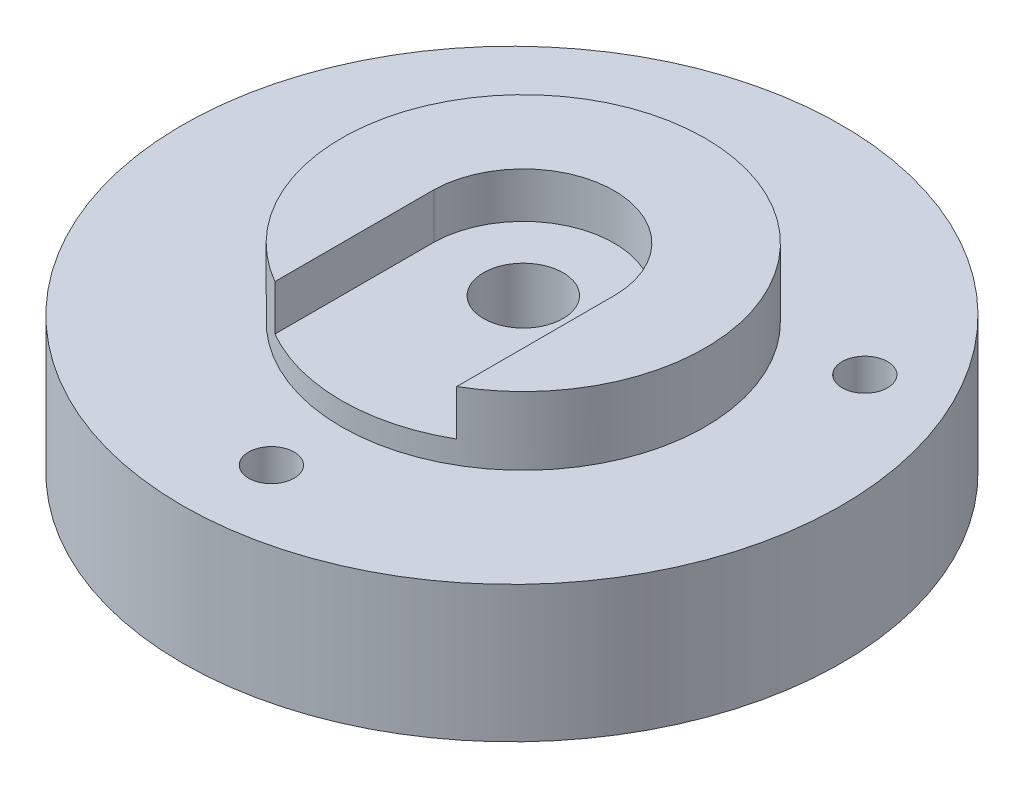
SolidWorks part; units mm, degrees
ref_plane "Front Plane" through (0, 0, 0) normal (0, 0, 1) x (1, 0, 0)
ref_plane "Top Plane" through (0, 0, 0) normal (0, 1, 0) x (1, 0, 0)
ref_plane "Right Plane" through (0, 0, 0) normal (1, 0, 0) x (0, 0, -1)
sketch "Sketch1" plane through (0, 0, 0) normal (0, 0, 1) x (1, 0, 0)
  line L1 (0, 0) -> (150, 0)
  line L2 (0, 0) -> (0, 30)
  line L3 (0, 30) -> (150, 30)
  line L4 (150, 0) -> (150, 30)
  line L5 (35, 30) -> (115, 30)
  line L6 (35, 30) -> (35, 45)
  line L7 (35, 45) -> (115, 45)
  line L8 (115, 30) -> (115, 45)
  dimension "D1" = 30
  dimension "D2" = 15
  dimension "D3" = 35
  dimension "D4" = 80
  dimension "D5" = 150
extrude "Boss-Extrude1" add sketch "Sketch1" along normal blind 145 contours L1 L4 L3 L2 | L3 L8 L7 L6
sketch "Sketch2" plane through (0, 0, 0) normal (0, 1, 0) x (1, 0, 0)
  line L1 (0, 0) -> (150, 0)
  line L2 (0, 0) -> (0, -145)
  line L3 (0, -145) -> (150, -145)
  line L4 (150, 0) -> (150, -145)
  circle A0 centre (72.5, -72.5) radius 72.5
  dimension "D1" = 145
  dimension "D2" = 72.5
  dimension "D3" = 72.5
extrude "Cut-Extrude1" cut sketch "Sketch2" along normal blind 145 contours A0 L1 L2 | A0 L2 L3 | A0 L3 L4 L1
sketch "Sketch3" plane through (0, 45, 0) normal (0, 1, 0) x (1, 0, 0)
  line L1 (35, -10.4516) -> (35, -134.5484)
  line L2 (115, -13.7633) -> (115, -131.2367)
  circle A0 centre (75, -72.5016) radius 40
  arc A1 (35, -10.4516) -> (115, -13.7633) centre (72.5, -72.5) cw
  arc A2 (35, -134.5484) -> (115, -131.2367) centre (72.5, -72.5) ccw
  arc A3 (115, -131.2367) -> (115, -13.7633) centre (72.5, -72.5) ccw construction
  arc A4 (35, -134.5484) -> (115, -131.2367) centre (72.5, -72.5) ccw construction
  arc A5 (115, -13.7633) -> (35, -10.4516) centre (72.5, -72.5) ccw construction
  line M1 (115, -131.2367) -> (115, -13.7633)
  arc M2 (115, -13.7633) -> (35, -10.4516) centre (72.5, -72.5) ccw
  line M3 (35, -10.4516) -> (35, -134.5484)
  arc M4 (35, -134.5484) -> (115, -131.2367) centre (72.5, -72.5) ccw
  dimension "D1" = 80
  dimension "D2" = 40
  dimension "D3" = 40
  dimension "D4" = 62.05
  dimension "D5" = 62.0467
extrude "Cut-Extrude2" cut sketch "Sketch3" against normal blind 15 contours A0 L2 M2 M3 | A0 L1 M4 M1
sketch "Sketch4" plane through (0, 45, 0) normal (0, 1, 0) x (1, 0, 0)
  line L0 (55, -107.1426) -> (55, -72.1426)
  line L1 (95, -107.1426) -> (95, -72.1426)
  circle A0 centre (75, -72.5016) radius 40 construction
  arc A1 (95, -107.1426) -> (55, -107.1426) centre (75, -72.5016) cw
  arc A4 (95, -72.1426) -> (55, -72.1426) centre (75, -72.5016) ccw
  circle M1 centre (75, -72.5016) radius 40
  dimension "D1" = 35
  dimension "D2" = 20
  dimension "D3" = 35
  dimension "D4" = 20
  dimension "D5" = 0
extrude "Cut-Extrude3" cut sketch "Sketch4" against normal blind 10 contours L1 A4 L0 M1
sketch "Sketch5" plane through (0, 35, 0) normal (0, 1, 0) x (1, 0, 0)
  point P0 (75, -72.5016)
hole_wizard "M20 Tapped Hole1" positions "3DSketch1" profile "Sketch6" tap size "M20" standard "ISO"
sketch3d "3DSketch1"
  point P0 (75, 35, 72.5016)
sketch "Sketch6" plane through (75, 35, 72.5016) normal (1, 0, 0) x (0, 0, 1)
  line L0 (0, 0) -> (0, 45.2575)
  line L1 (0, 45.2575) -> (8.75, 40)
  line L2 (8.75, 40) -> (8.75, 0)
  line L5 (8.75, 0) -> (0, 0)
  line L10 (0, 45.2575) -> (-8.75, 40) construction
  line L11 (0, -6.35) -> (0, 107.95) construction
  dimension "Tap Drill Dia." = 17.5
  dimension "Tap Drill Depth" = 40
  dimension "Drill Angle" = 118
cosmetic thread "Hole Thread1" parameters "D1"=20, "D2"=20
sketch "Sketch7" plane through (0, 0, 0) normal (0, 1, 0) x (1, 0, 0)
  line L0 (74.5832, 4.1452) -> (74.5832, -159.0835) construction
  line L1 (0, -72.5) -> (161.2663, -72.5) construction
  line L2 (75, -72.5016) -> (150.2505, -29.0558) construction
  line L3 (75, -72.5016) -> (-21.1007, -17.0179) construction
  circle A0 centre (72.5, -72.5) radius 72.5 construction
  circle A1 centre (74.5832, -127.5016) radius 5
  circle A2 centre (27.3686, -45.0016) radius 5
  circle A3 centre (122.6314, -45.0016) radius 5
  dimension "D2" = 10
  dimension "D7" = 10
  dimension "D8" = 10
  dimension "D1" = 74.5832
  dimension "D3" = 55
  dimension "D4" = 120
  dimension "D5" = 55.4837
  dimension "D6" = 120
  dimension "D9" = 55
  dimension "D10" = 55
extrude "Cut-Extrude4" cut sketch "Sketch7" along normal blind 83
sketch "Sketch8" plane through (0, 0, 0) normal (0, -1, 0) x (1, 0, 0)
  circle A0 centre (75, 72.5016) radius 55
  dimension "D1" = 110
extrude "Cut-Extrude5" cut sketch "Sketch8" against normal blind 15
